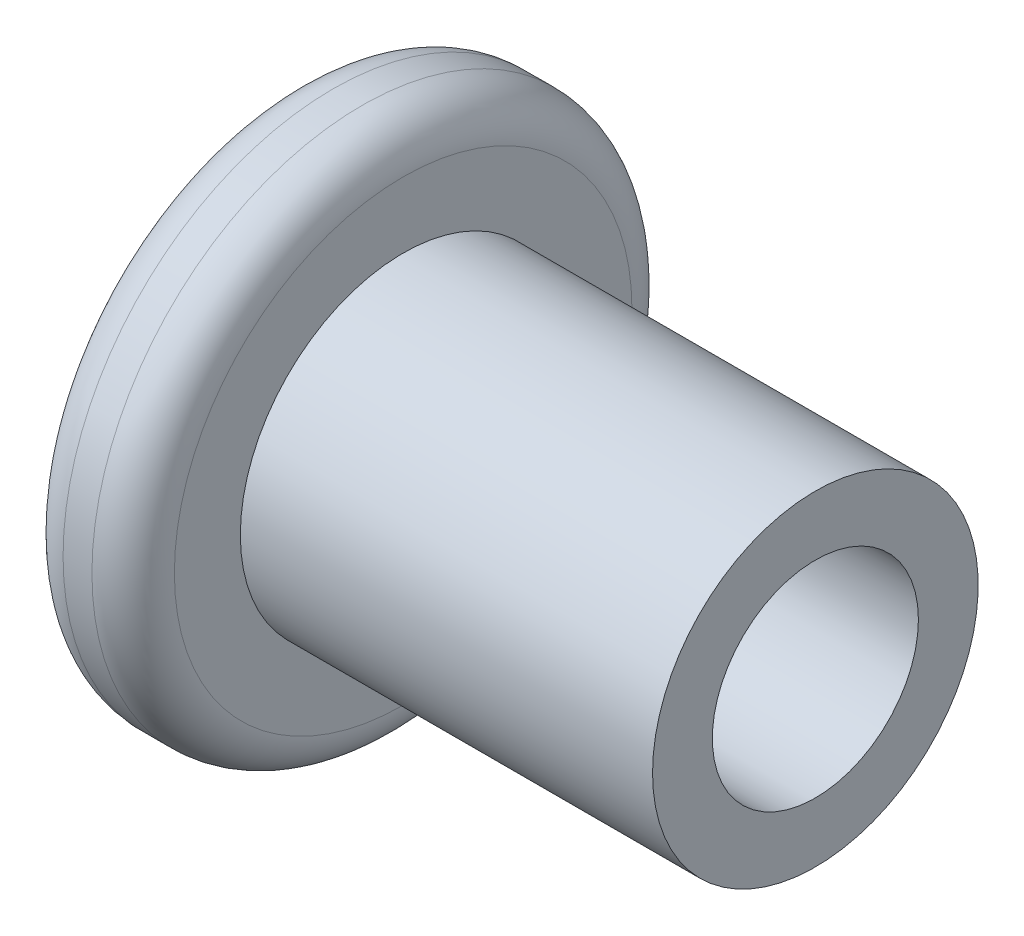
SolidWorks part; units mm, degrees
material "AISI 304"
ref_plane "前视基准面" through (0, 0, 0) normal (0, 0, 1) x (1, 0, 0)
ref_plane "上视基准面" through (0, 0, 0) normal (0, 1, 0) x (1, 0, 0)
ref_plane "右视基准面" through (0, 0, 0) normal (1, 0, 0) x (0, 0, -1)
sketch "草图1" plane through (0, 0, 0) normal (0, 0, 1) x (1, 0, 0)
  line L0 (0, 0) -> (12.7, 0) construction
  line L1 (0, 0) -> (0, 6.55)
  line L2 (0, 6.55) -> (2.7, 6.55)
  line L3 (2.7, 6.55) -> (2.7, 3.95)
  line L4 (2.7, 3.95) -> (12.7, 3.95)
  line L5 (12.7, 3.95) -> (12.7, 0)
  line L6 (0, 0) -> (12.7, 0)
  dimension "D1" = 6.55
  dimension "D2" = 2.7
  dimension "D3" = 7.9
  dimension "D4" = 10
revolve "旋转1" add sketch "草图1" angle 360 about L0
fillet "圆角1" radius 1 2 edges at (2.7, 0, 6.55) (0, 0, 6.55)
sketch "草图2" plane through (0, 0, 0) normal (-1, 0, 0) x (0, 0, 1)
  line L1 (1.1547, 2) -> (-1.1547, 2)
  line L2 (-1.1547, 2) -> (-2.3094, 0)
  line L3 (-2.3094, 0) -> (-1.1547, -2)
  line L4 (-1.1547, -2) -> (1.1547, -2)
  line L5 (1.1547, -2) -> (2.3094, 0)
  line L6 (2.3094, 0) -> (1.1547, 2)
  circle A0 centre (0, 0) radius 2 construction
  dimension "D1" = 4
extrude "切除-拉伸1" cut sketch "草图2" against normal blind 1
hole_wizard "M6 螺纹孔1" positions "草图4" profile "草图5" tap size "M6" standard "GB"
sketch "草图4" plane through (12.7, 0, 0) normal (1, 0, 0) x (0, 0, -1)
  point P0 (0, 0)
sketch "草图5" plane through (12.7, 0, 0) normal (0, 1, 0) x (0, 0, -1)
  line L0 (0, 0) -> (0, 5.6022)
  line L1 (0, 5.6022) -> (2.5, 4.1)
  line L2 (2.5, 4.1) -> (2.5, 0)
  line L5 (2.5, 0) -> (0, 0)
  line L10 (0, 5.6022) -> (-2.5, 4.1) construction
  line L11 (0, -6.35) -> (0, 107.95) construction
  dimension "螺纹孔钻头直径" = 5
  dimension "螺纹孔钻头深度" = 4.1
  dimension "导头角度" = 118
cosmetic thread "孔螺蚊线1" parameters "D1"=5.6, "D2"=6
sketch "草图6" plane through (12.7, 0, 0) normal (1, 0, 0) x (0, 0, -1)
  circle A1 centre (0, 0) radius 3.95
  circle A2 centre (0, 0) radius 3.95
  dimension "D1" = 0
